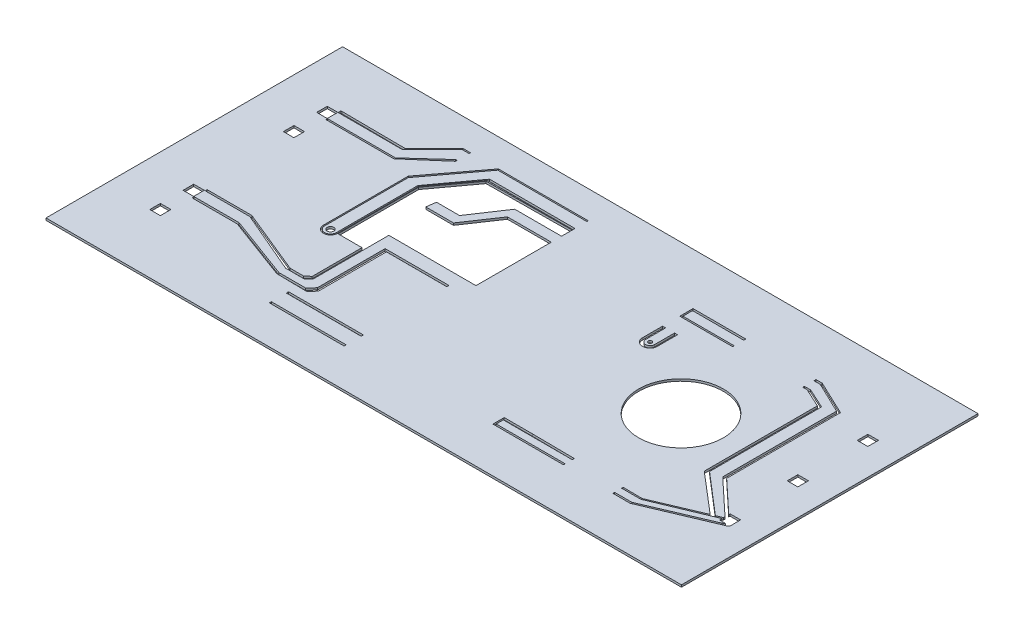
SolidWorks part; units mm, degrees
ref_plane "Front" through (0, 0, 0) normal (0, 0, 1) x (1, 0, 0)
ref_plane "Top" through (0, 0, 0) normal (0, 1, 0) x (1, 0, 0)
ref_plane "Right" through (0, 0, 0) normal (1, 0, 0) x (0, 0, -1)
sketch "Sketch1" plane through (0, 0, 0) normal (0, 1, 0) x (1, 0, 0)
  line L0 (-30, 0) -> (0, 0)
  line L2 (0, 0) -> (0, 14)
  line L3 (0, 14) -> (-30, 14)
  line L4 (-30, 0) -> (-30, 14)
  line L5 (0, 0) -> (-30, 14) construction
  line L6 (0, 14) -> (-30, 0) construction
  line L7 (-1.2567, 10.055) -> (-1.7559, 10.055)
  line L8 (-1.2565, 6.7493) -> (-1.7557, 6.7493)
  line L9 (-1.2565, 6.7493) -> (-1.2565, 7.2507)
  line L10 (-1.2565, 7.2507) -> (-1.7557, 7.2507)
  line L11 (-1.7557, 6.7493) -> (-1.7557, 7.2507)
  line L12 (-1.2565, 6.7493) -> (-1.7557, 7.2507) construction
  line L13 (-1.2565, 7.2507) -> (-1.7557, 6.7493) construction
  line L14 (-1.2567, 10.055) -> (-1.2567, 10.5565)
  line L15 (-1.2567, 10.5565) -> (-1.7559, 10.5565)
  line L16 (-1.7559, 10.055) -> (-1.7559, 10.5565)
  line L18 (-1.2565, 3.5505) -> (-1.2814, 3.5505)
  line L19 (-1.2565, 3.5505) -> (-1.2565, 4.0519)
  line L20 (-1.2565, 4.0519) -> (-1.7557, 4.0519)
  line L21 (-1.7557, 3.5505) -> (-1.7557, 3.6634)
  line L33 (-20.7407, 3.5558) -> (-20.7407, 6.7512)
  line L63 (-21.1967, 7.2507) -> (-21.1967, 4.16)
  line L93 (-27.3947, 2.7937) -> (-27.8939, 2.7937)
  line L94 (-27.3947, 2.7937) -> (-27.3947, 3.2952)
  line L95 (-27.3947, 3.2952) -> (-27.8939, 3.2952)
  line L96 (-27.8939, 2.7937) -> (-27.8939, 3.2952)
  line L98 (-27.3947, 4.3663) -> (-27.8939, 4.3663)
  line L99 (-27.3947, 4.3663) -> (-27.3947, 4.8678)
  line L100 (-27.3947, 4.8678) -> (-27.8939, 4.8678)
  line L101 (-27.8939, 4.3663) -> (-27.8939, 4.8678)
  line L117 (-27.4283, 9.1322) -> (-27.9275, 9.1322)
  line L118 (-27.4283, 9.1322) -> (-27.4283, 9.6337)
  line L119 (-27.4283, 9.6337) -> (-27.9275, 9.6337)
  line L120 (-27.9275, 9.1322) -> (-27.9275, 9.6337)
  line L121 (-27.4283, 10.7048) -> (-27.9275, 10.7048)
  line L122 (-27.4283, 10.7048) -> (-27.4283, 11.2063)
  line L123 (-27.4283, 11.2063) -> (-27.9275, 11.2063)
  line L124 (-27.9275, 10.7048) -> (-27.9275, 11.2063)
  line L141 (-27.3503, 11.2063) -> (-24.3914, 11.2063)
  line L142 (-24.3914, 11.2063) -> (-22.9784, 12.6192)
  line L143 (-22.9784, 12.6192) -> (-22.6494, 12.6192)
  line L144 (-21.3272, 3.8952) -> (-21.3272, 6.2447)
  line L145 (-22.6494, 12.056) -> (-22.7212, 12.056)
  line L146 (-27.3503, 10.7048) -> (-24.2075, 10.7048)
  line L147 (-24.2075, 10.7048) -> (-22.7212, 12.056)
  line L166 (-27.3503, 10.629) -> (-24.2075, 10.629)
  line L167 (-24.2075, 10.629) -> (-22.6876, 11.9478)
  line L168 (-22.6876, 11.9478) -> (-22.6494, 11.9478)
  line L171 (-22.6494, 12.6846) -> (-23.0005, 12.6846)
  line L172 (-23.0005, 12.6846) -> (-24.2061, 11.479)
  line L178 (-27.2805, 4.27) -> (-25.2451, 4.27)
  line L180 (-25.2451, 4.3663) -> (-27.2805, 4.3663)
  line L181 (-27.2805, 4.8678) -> (-25.2451, 4.8678)
  line L183 (-25.2451, 4.9608) -> (-27.2805, 4.9608)
  line L184 (-25.2451, 4.27) -> (-22.2754, 3.1709)
  line L185 (-25.2451, 4.3663) -> (-22.2688, 3.2648)
  line L186 (-25.2451, 4.8678) -> (-22.2897, 3.6017)
  line L210 (-20.5771, 6.5887) -> (-20.5771, 3.4344)
  line L212 (-17.7261, 6.6488) -> (-17.7261, 6.7512)
  line L213 (-17.7261, 6.7512) -> (-20.7407, 6.7512)
  line L214 (-20.5771, 7.3824) -> (-17.7261, 7.3824)
  line L218 (-21.1967, 7.2507) -> (-21.1967, 7.3824)
  line L219 (-21.1967, 7.3824) -> (-20.5771, 7.3824)
  line L222 (-20.5771, 6.5887) -> (-20.5771, 6.6488)
  line L223 (-20.5771, 6.6488) -> (-17.7261, 6.6488)
  line L224 (-22.2897, 3.6017) -> (-21.398, 3.6017)
  line L225 (-22.1779, 3.707) -> (-21.5528, 3.707)
  line L227 (-22.1779, 3.707) -> (-25.2451, 4.9608)
  line L229 (-21.1967, 3.8011) -> (-21.1967, 4.16)
  line L231 (-22.2688, 3.2648) -> (-21.0064, 3.2648)
  line L232 (-21.2566, 2.7086) -> (-20.5771, 2.7086)
  line L234 (-20.5771, 2.6021) -> (-21.2566, 2.6021)
  line L235 (-21.2566, 2.6021) -> (-21.2566, 2.7086)
  line L236 (-20.5771, 2.7086) -> (-17.7261, 2.7086)
  line L237 (-17.7261, 2.7086) -> (-17.7261, 2.6021)
  line L238 (-17.7261, 2.6021) -> (-20.5771, 2.6021)
  line L239 (-21.2566, 1.8969) -> (-17.7261, 1.8969)
  line L240 (-17.7261, 1.8969) -> (-17.7261, 1.8004)
  line L241 (-17.7261, 1.8004) -> (-21.2566, 1.8004)
  line L242 (-21.2566, 1.8004) -> (-21.2566, 1.8969)
  line L246 (-22.5477, 9.6354) -> (-22.5477, 6.231)
  line L249 (-23.0982, 9.6354) -> (-23.0982, 6.2554)
  line L250 (-23.1582, 9.6354) -> (-23.1582, 6.2554)
  line L256 (-23.1582, 9.6354) -> (-23.1582, 10.2602)
  line L258 (-23.0982, 10.1972) -> (-23.0982, 9.6354)
  line L259 (-22.5477, 9.6354) -> (-22.5477, 10.0992)
  line L273 (-17.0826, 12.056) -> (-21.1171, 12.056)
  line L274 (-21.2855, 12.6192) -> (-17.0826, 12.6192)
  line L275 (-21.3272, 12.6846) -> (-17.0826, 12.6846)
  line L283 (-23.0982, 10.1972) -> (-21.2855, 12.6192)
  line L284 (-23.1582, 10.2602) -> (-21.3272, 12.6846)
  line L285 (-22.6494, 11.9478) -> (-22.6494, 12.056)
  line L287 (-22.6494, 12.6192) -> (-22.6494, 12.6846)
  line L289 (-21.1171, 12.056) -> (-22.5477, 10.0992)
  line L296 (-17.1224, 11.422) -> (-19.2931, 11.422)
  line L301 (-17.1224, 10.9375) -> (-19.1529, 10.9375)
  line L309 (-20.1763, 9.4156) -> (-19.1529, 10.9375)
  line L313 (-24.2061, 11.479) -> (-24.3655, 11.3195)
  line L314 (-24.3655, 11.3195) -> (-27.3503, 11.3426)
  line L315 (-20.3352, 9.8608) -> (-19.2931, 11.422)
  line L318 (-20.3352, 9.8608) -> (-21.4238, 9.8608)
  line L323 (-21.4864, 9.4156) -> (-20.1763, 9.4156)
  line L326 (-17.0826, 12.6846) -> (-17.0826, 12.6192)
  line L327 (-17.0826, 11.926) -> (-17.0826, 11.5111)
  line L331 (-22.4619, 6.2447) -> (-21.3272, 6.2447)
  line L332 (-21.4864, 9.4156) -> (-21.4238, 9.8608)
  line L335 (-22.4868, 6.2447) -> (-22.4868, 10.0992)
  line L336 (-22.4868, 10.0992) -> (-21.1171, 11.9478)
  line L337 (-21.1171, 11.9478) -> (-17.0826, 11.9478)
  line L346 (-17.0826, 10.8799) -> (-17.0826, 7.3824)
  line L348 (-22.4619, 6.2447) -> (-22.4619, 10.055)
  line L349 (-22.4619, 10.055) -> (-21.1171, 11.8894)
  line L350 (-21.1171, 11.8894) -> (-17.0826, 11.926)
  line L351 (-17.0826, 11.9478) -> (-17.0826, 12.056)
  line L352 (-17.7261, 7.3824) -> (-17.0826, 7.3824)
  line L353 (-17.1224, 10.9375) -> (-17.0826, 10.9375)
  line L355 (-17.0826, 11.422) -> (-17.1224, 11.422)
  line L356 (-17.0826, 10.8799) -> (-17.0826, 10.9375)
  line L357 (-17.0826, 11.422) -> (-17.0826, 11.5111)
  line L358 (-1.335, 3.4812) -> (-4.5469, 2.1219)
  line L359 (-4.5469, 2.1219) -> (-5.3603, 2.1219)
  line L361 (-9.6765, 2.6554) -> (-7.6903, 2.6351)
  line L362 (-4.4533, 2.6021) -> (-2.1999, 3.5558)
  line L365 (-5.3603, 2.1219) -> (-5.3603, 2.2038)
  line L368 (-7.6903, 2.1219) -> (-9.7234, 2.1219)
  line L369 (-5.3603, 2.6114) -> (-4.4533, 2.6021)
  line L370 (-11.0223, 2.6554) -> (-9.6765, 2.6554)
  line L371 (-9.7234, 2.1219) -> (-11.0223, 2.1219)
  line L373 (-7.6903, 2.1219) -> (-7.6903, 2.2038)
  line L374 (-11.0223, 2.1219) -> (-11.0223, 2.6554)
  line L375 (-11.0223, 9.1871) -> (-11.0223, 10.1323)
  line L378 (-10.8766, 9.1871) -> (-10.8766, 10.1323)
  line L379 (-10.4579, 9.1871) -> (-10.4579, 10.1323)
  line L381 (-11.0223, 11.5679) -> (-8.5275, 11.5679)
  line L384 (-4.9222, 11.4718) -> (-5.2152, 11.4718)
  line L385 (-11.0223, 10.9437) -> (-8.5275, 10.9437)
  line L387 (-11.0223, 10.1323) -> (-10.8766, 10.1323)
  line L390 (-10.4579, 10.1323) -> (-10.3176, 10.1323)
  line L391 (-10.3176, 10.1323) -> (-10.3176, 9.1253)
  line L392 (-11.0223, 10.9437) -> (-11.0223, 11.2662)
  line L393 (-10.9488, 11.0191) -> (-8.6178, 11.0191)
  line L395 (-11.0223, 11.2662) -> (-11.0223, 11.5679)
  line L396 (-10.9488, 11.4718) -> (-10.9488, 11.0191)
  line L397 (-10.9488, 2.2038) -> (-7.6903, 2.2038)
  line L398 (-10.9488, 2.2038) -> (-10.9488, 2.5379)
  line L399 (-7.6903, 2.5379) -> (-10.9488, 2.5379)
  line L400 (-5.3603, 2.2038) -> (-4.5469, 2.2038)
  line L401 (-4.5469, 2.2038) -> (-1.5584, 3.4812)
  line L402 (-1.7817, 3.6524) -> (-4.4533, 2.5379)
  line L403 (-4.4533, 2.5379) -> (-5.3603, 2.5379)
  line L404 (-5.3603, 2.5379) -> (-5.3603, 2.6114)
  line L405 (-7.6903, 2.5379) -> (-7.6903, 2.6351)
  line L407 (-5.2152, 10.9437) -> (-5.2152, 11.0191)
  line L408 (-8.5275, 10.9437) -> (-8.5275, 11.0191)
  line L409 (-4.9222, 11.5679) -> (-3.2863, 10.7938)
  line L410 (-8.6178, 11.4718) -> (-10.9488, 11.4718)
  line L411 (-5.2152, 10.9437) -> (-5.0118, 10.9437)
  line L412 (-5.2152, 11.0191) -> (-4.9222, 11.0191)
  line L413 (-3.2863, 10.7938) -> (-3.2863, 5.4209)
  line L414 (-5.2152, 11.4718) -> (-5.2152, 11.5679)
  line L415 (-5.2152, 11.5679) -> (-4.9222, 11.5679)
  line L416 (-3.2863, 5.4209) -> (-1.8241, 4.0519)
  line L418 (-1.8241, 3.8759) -> (-3.4402, 5.389)
  line L419 (-3.4402, 5.389) -> (-3.4402, 10.7614)
  line L420 (-3.4402, 10.7614) -> (-4.9222, 11.4718)
  line L421 (-4.9222, 11.0191) -> (-3.968, 10.5836)
  line L422 (-3.968, 10.5836) -> (-3.968, 5.2942)
  line L423 (-3.968, 5.2942) -> (-2.0549, 3.6524)
  line L425 (-2.231, 3.5823) -> (-4.1099, 5.1863)
  line L426 (-4.1099, 5.1863) -> (-4.1099, 10.5263)
  line L427 (-4.1099, 10.5263) -> (-5.0118, 10.9437)
  line L428 (-2.231, 3.5823) -> (-2.1999, 3.5558)
  line L429 (-2.0271, 3.6289) -> (-1.7817, 3.7328)
  line L430 (-2.0271, 3.6289) -> (-2.0549, 3.6524)
  line L431 (-1.8241, 3.8759) -> (-1.7557, 3.8118)
  line L432 (-1.7557, 3.9878) -> (-1.7557, 4.0519)
  line L433 (-1.8241, 4.0519) -> (-1.7557, 3.9878)
  line L434 (-1.7817, 3.7328) -> (-1.7557, 3.7438)
  line L436 (-1.7817, 3.6524) -> (-1.7557, 3.6634)
  line L437 (-1.7557, 3.7438) -> (-1.7557, 3.8118)
  line L438 (-1.5584, 3.4812) -> (-1.4721, 3.5505)
  line L440 (-1.2814, 3.5505) -> (-1.335, 3.4812)
  line L441 (-1.4721, 3.5505) -> (-1.7557, 3.5505)
  line L442 (-8.6178, 11.0191) -> (-8.5275, 11.0191)
  line L443 (-8.5275, 11.4718) -> (-8.5275, 11.5679)
  line L444 (-8.5275, 11.4718) -> (-8.6178, 11.4718)
  line L445 (-27.4171, 11.2063) -> (-27.3503, 11.2063)
  line L446 (-27.3503, 11.3426) -> (-27.4171, 11.3426)
  line L447 (-27.4171, 11.3426) -> (-27.4171, 11.2063)
  line L448 (-27.3503, 10.7048) -> (-27.4171, 10.7048)
  line L449 (-27.4171, 10.7048) -> (-27.4171, 10.629)
  line L450 (-27.4171, 10.629) -> (-27.3503, 10.629)
  line L451 (-27.2805, 4.3663) -> (-27.3716, 4.3663)
  line L452 (-27.3716, 4.3663) -> (-27.3716, 4.27)
  line L453 (-27.3716, 4.27) -> (-27.2805, 4.27)
  line L454 (-27.2805, 4.8678) -> (-27.3503, 4.8678)
  line L455 (-27.3503, 4.8678) -> (-27.3503, 4.9608)
  line L456 (-27.3503, 4.9608) -> (-27.2805, 4.9608)
  line L463 (-22.2754, 3.1709) -> (-20.8394, 3.1472)
  line L465 (-21.5528, 3.707) -> (-21.3272, 3.8952)
  line L467 (-21.398, 3.6017) -> (-21.1967, 3.8011)
  line L469 (-21.0064, 3.2648) -> (-20.7407, 3.5558)
  line L471 (-20.8394, 3.1472) -> (-20.5771, 3.4344)
  circle A0 centre (-7.0204, 7) radius 2
  arc A2 (-23.0982, 6.2554) -> (-22.5477, 6.231) centre (-22.8224, 6.2554) ccw
  arc A3 (-23.1582, 6.2554) -> (-22.4868, 6.2447) centre (-22.8224, 6.2554) ccw
  circle A4 centre (-22.8224, 6.2554) radius 0.156
  arc A6 (-11.0223, 9.1871) -> (-10.3176, 9.1253) centre (-10.6672, 9.1871) ccw
  arc A7 (-10.8766, 9.1871) -> (-10.4579, 9.1871) centre (-10.6672, 9.1871) ccw
  circle A8 centre (-10.6672, 9.1871) radius 0.0862
  point P4 (-15, 7)
  point P13 (-1.5061, 7)
  dimension "D1" = 30
  dimension "D2" = 14
extrude "Boss-Extrude2" add sketch "Sketch1" along normal blind 0.1
